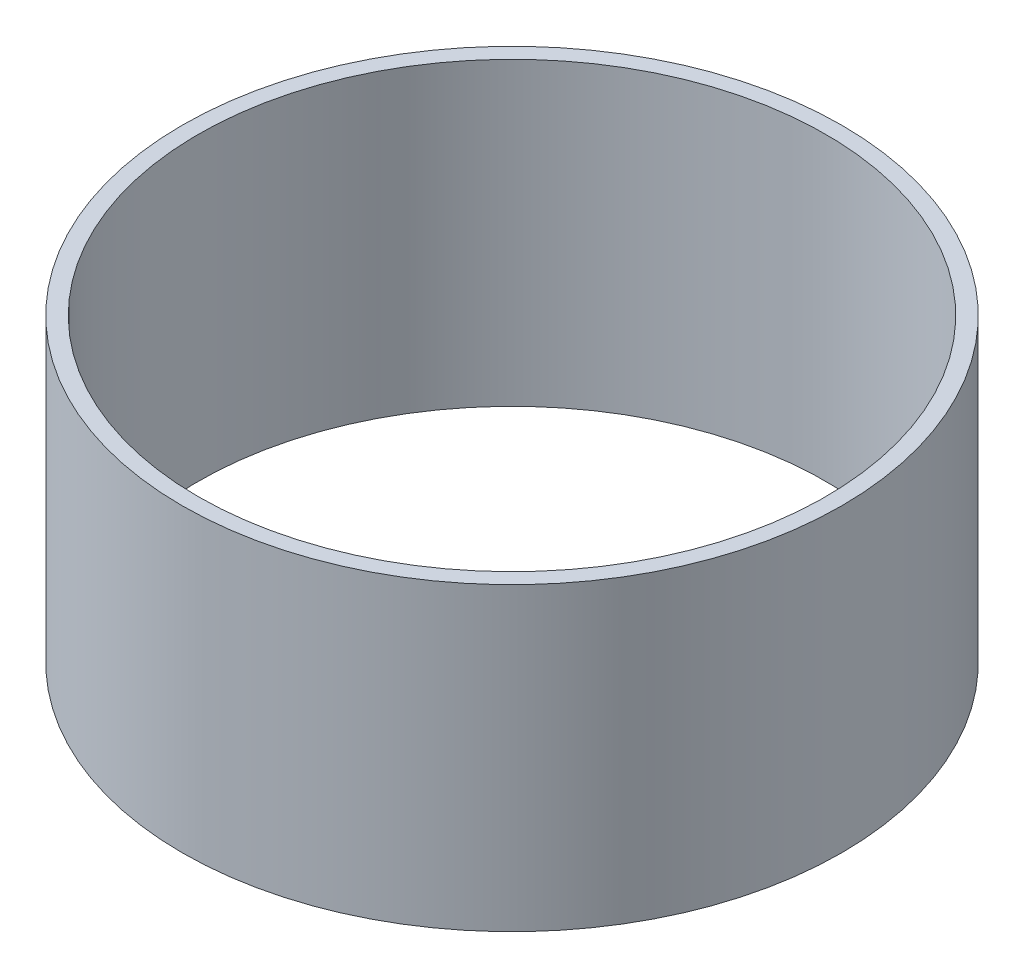
SolidWorks part; units mm, degrees
ref_plane "前视基准面" through (0, 0, 0) normal (0, 0, 1) x (1, 0, 0)
ref_plane "上视基准面" through (0, 0, 0) normal (0, 1, 0) x (1, 0, 0)
ref_plane "右视基准面" through (0, 0, 0) normal (1, 0, 0) x (0, 0, -1)
sketch "草图1" plane through (0, 0, 0) normal (0, 1, 0) x (1, 0, 0)
  circle A0 centre (0, 0) radius 735
  dimension "D1" = 1470
extrude "凸台-拉伸1" add sketch "草图1" along normal blind 670
sketch "草图2" plane through (0, 670, 0) normal (0, 1, 0) x (1, 0, 0)
  circle A0 centre (0, 0) radius 699.5
  dimension "D1" = 1399
extrude "切除-拉伸1" cut sketch "草图2" against normal blind 3178
